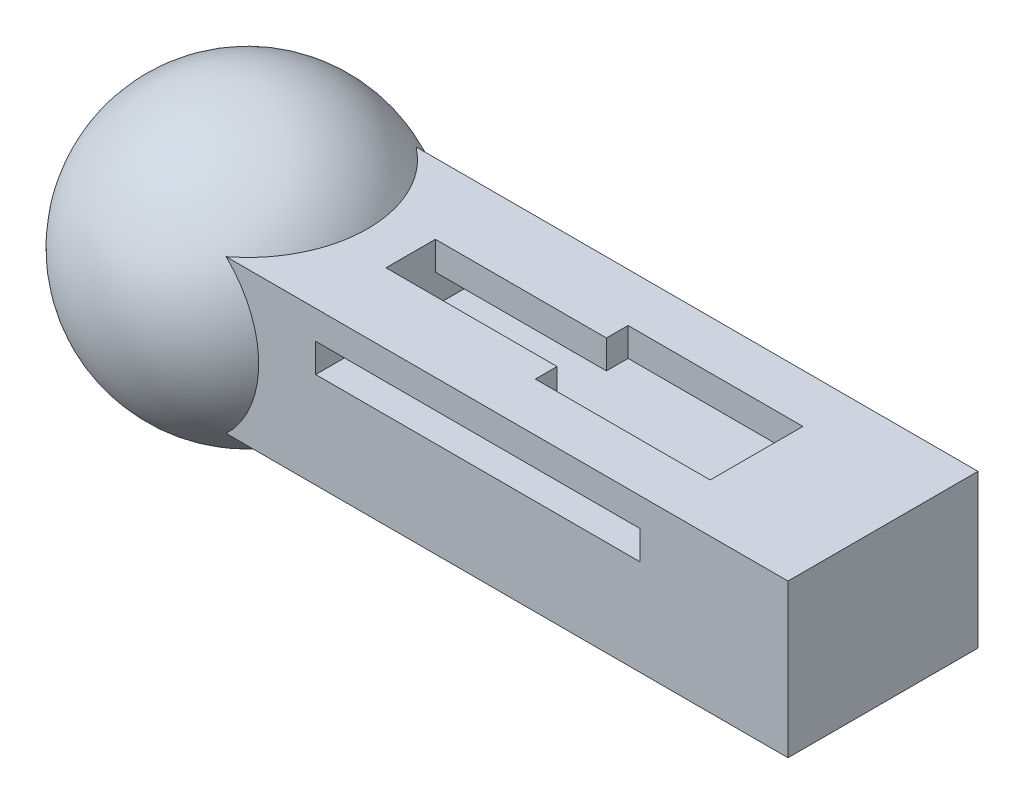
SolidWorks part; units mm, degrees
ref_plane "Alzado" through (0, 0, 0) normal (0, 0, 1) x (1, 0, 0)
ref_plane "Planta" through (0, 0, 0) normal (0, 1, 0) x (1, 0, 0)
ref_plane "Vista lateral" through (0, 0, 0) normal (1, 0, 0) x (0, 0, -1)
sketch "Croquis2" plane through (0, 0, 0) normal (0, 0, 1) x (1, 0, 0)
  line L1 (0, 0) -> (17.067, 0)
  line L2 (0, 0) -> (0, 4.5554)
  line L3 (0, 4.5554) -> (17.067, 4.5554)
  line L4 (17.067, 0) -> (17.067, 4.5554)
  line L5 (-1.8893, -2) -> (24.8544, -2)
  line L6 (-1.8893, -2) -> (-1.8893, 6.0554)
  line L7 (-1.8893, 6.0554) -> (24.8544, 6.0554)
  line L8 (24.8544, -2) -> (24.8544, 6.0554)
  dimension "D1" = 2
  dimension "D2" = 1.5
  dimension "D3" = 4.5554
extrude "Saliente-Extruir1" add sketch "Croquis2" along normal mid plane 10
sketch "Croquis3" plane through (0, 6.0554, 0) normal (0, 1, 0) x (1, 0, 0)
  line L0 (0, 0) -> (22.7193, 0) construction
  line L1 (9, -2.4402) -> (9, -1.3)
  line L2 (18.2, 2.4402) -> (9, 2.4402)
  line L3 (18.2, 2.4402) -> (18.2, -2.4402)
  line L4 (18.2, -2.4402) -> (9, -2.4402)
  line L5 (0, 2.4402) -> (0, 1.3)
  line L6 (18.2, 2.4402) -> (0, -2.4402) construction
  line L7 (18.2, -2.4402) -> (0, 2.4402) construction
  line L8 (0, -1.3) -> (0, -2.4402)
  line L9 (0, -1.3) -> (9, -1.3)
  line L10 (0, -1.3) -> (0, 1.3)
  line L11 (0, 1.3) -> (9, 1.3)
  line L12 (9, -0.0268) -> (9, 0.0268)
  line L13 (9, 1.3) -> (9, 2.4402)
  line L14 (9, -0.0268) -> (9, 0.0268)
  point P3 (9.1, 0)
  dimension "D1" = 18.2
  dimension "D2" = 9
  dimension "D3" = 2.6
extrude "Cortar-Extruir1" cut sketch "Croquis3" against normal up to surface (6.0554 mm away) up to face at (8.5335, 0, 0)
sketch "Croquis4" plane through (0, 0, 0) normal (0, 1, 0) x (1, 0, 0)
  line L8 (17.067, 5) -> (0, 5)
  line L9 (0, 5) -> (0, -5)
  line L10 (0, -5) -> (17.067, -5)
  line L11 (17.067, -5) -> (17.067, -2.4402)
  line L12 (17.067, -2.4402) -> (18.2, -2.4402)
  line L13 (18.2, -2.4402) -> (18.2, 2.4402)
  line L14 (18.2, 2.4402) -> (17.067, 2.4402)
  line L15 (17.067, 2.4402) -> (17.067, 5)
  line L16 (17.067, 5) -> (0, 5)
  line L17 (0, 5) -> (0, -5)
  line L18 (0, -5) -> (17.067, -5)
  line L19 (17.067, -5) -> (17.067, -2.4402)
  line L20 (17.067, -2.4402) -> (18.2, -2.4402)
  line L21 (18.2, -2.4402) -> (18.2, 2.4402)
  line L22 (18.2, 2.4402) -> (17.067, 2.4402)
  line L23 (17.067, 2.4402) -> (17.067, 5)
  dimension "D1" = 0
extrude "Saliente-Extruir2" add sketch "Croquis4" along normal blind 3.04
sketch "Croquis5" plane through (0, 6.0554, 0) normal (0, 1, 0) x (1, 0, 0)
  line L0 (-1.8893, 0) -> (24.8544, 0) construction
  line L1 (-1.8893, -5) -> (-1.8893, 5) construction
  line L2 (24.8544, -5) -> (24.8544, 5) construction
sketch "Croquis6" plane through (0, 0, 0) normal (0, 0, 1) x (1, 0, 0)
  line L0 (-1.8893, 2.0277) -> (-10.8972, 2.0277) construction
  line L1 (-1.8893, 6.0554) -> (-1.8893, -2) construction
  line L3 (-1.0882, 2.0277) -> (-16.0882, 2.0277)
  arc A0 (-1.0882, 2.0277) -> (-16.0882, 2.0277) centre (-8.5882, 2.0277) ccw
  dimension "D1" = 15
revolve "Revolución1" add sketch "Croquis6" angle 360 about L0
sketch "Croquis7" plane through (-1.8893, 0, 0) normal (-1, 0, 0) x (0, 0, 1)
  line L4 (-5, 6.0554) -> (-5, -2)
  line L5 (-5, -2) -> (5, -2)
  line L6 (5, -2) -> (5, 6.0554)
  line L7 (5, 6.0554) -> (-5, 6.0554)
  line L8 (-5, 6.0554) -> (-5, -2)
  line L9 (-5, -2) -> (5, -2)
  line L10 (5, -2) -> (5, 6.0554)
  line L11 (5, 6.0554) -> (-5, 6.0554)
  dimension "D1" = 0
extrude "Saliente-Extruir3" add sketch "Croquis7" along normal blind 3.04
